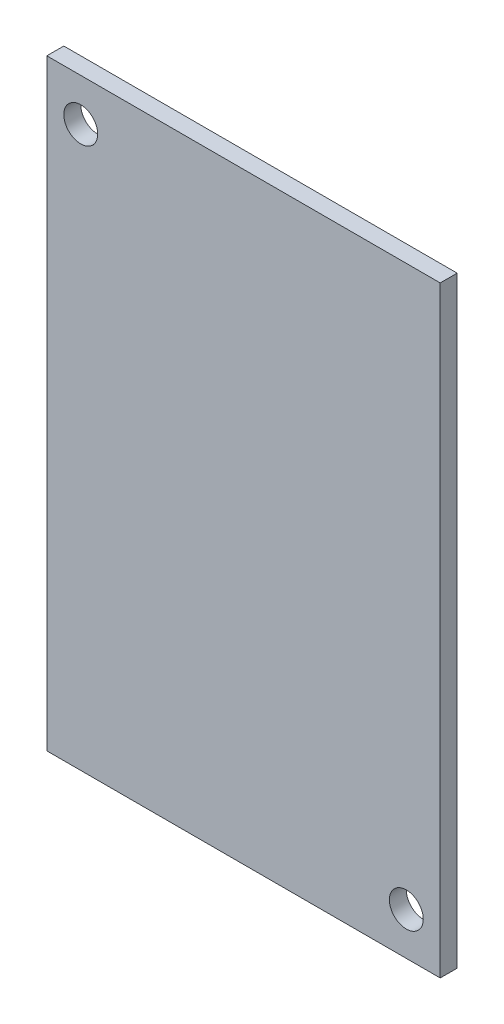
SolidWorks part; units mm, degrees
material "PP copolymère"
ref_plane "Face" through (0, 0, 0) normal (0, 0, 1) x (1, 0, 0)
ref_plane "Dessus" through (0, 0, 0) normal (0, 1, 0) x (1, 0, 0)
ref_plane "Droite" through (0, 0, 0) normal (1, 0, 0) x (0, 0, -1)
sketch "Esquisse1" plane through (0, 0, 0) normal (0, 0, 1) x (1, 0, 0)
  line L0 (0, 0) -> (33.0541, 0) construction
  line L1 (-23.2, 35.5) -> (23.2, 35.5)
  line L2 (-23.2, 35.5) -> (-23.2, -35.5)
  line L3 (-23.2, -35.5) -> (23.2, -35.5)
  line L4 (23.2, 35.5) -> (23.2, -35.5)
  line L5 (0, 0) -> (0, 31.1956) construction
  dimension "D1" = 46.4
  dimension "D2" = 71
extrude "Extrusion1" add sketch "Esquisse1" along normal blind 2
sketch "Esquisse2" plane through (0, 0, 2) normal (0, 0, 1) x (1, 0, 0)
  line L0 (0, 0) -> (0, 28.1312) construction
  line L1 (23.2, 35.5) -> (-23.2, 35.5) construction
  line L2 (-23.2, -35.5) -> (23.2, -35.5) construction
  circle A0 centre (-19.2, 30.5) radius 2
  circle A1 centre (19.2, -30.5) radius 2
  dimension "D1" = 4
  dimension "D4" = 4
  dimension "D2" = 19.2
  dimension "D3" = 5
  dimension "D5" = 5
  dimension "D6" = 19.2
extrude "Enlèv. mat.-Extru.1" cut sketch "Esquisse2" against normal through all
